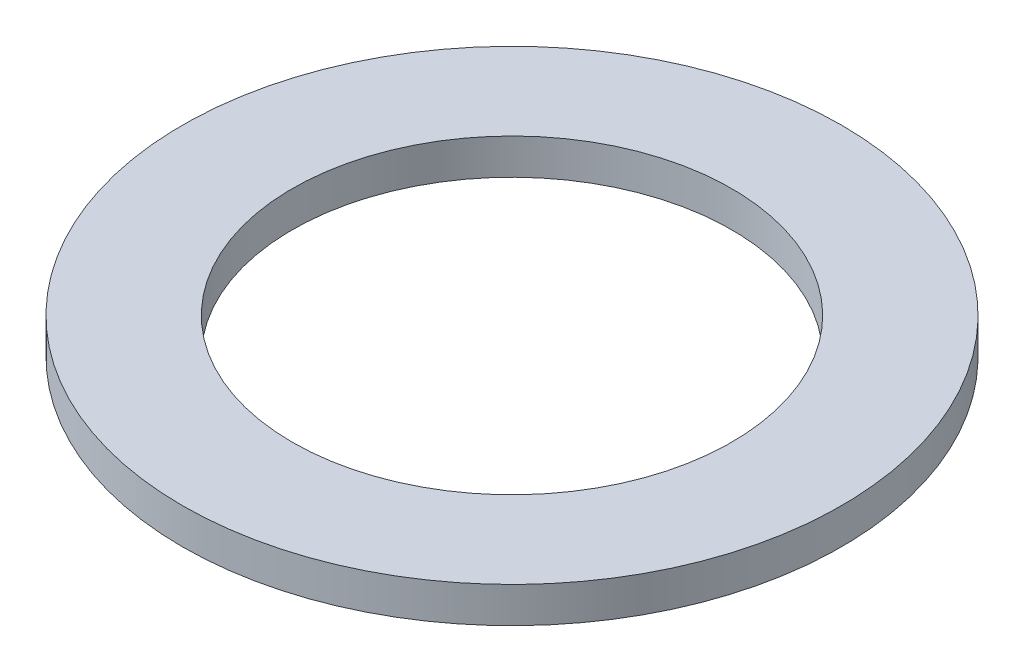
SolidWorks part; units mm, degrees
ref_plane "Front Plane" through (0, 0, 0) normal (0, 0, 1) x (1, 0, 0)
ref_plane "Top Plane" through (0, 0, 0) normal (0, 1, 0) x (1, 0, 0)
ref_plane "Right Plane" through (0, 0, 0) normal (1, 0, 0) x (0, 0, -1)
sketch "Sketch1" plane through (0, 0, 0) normal (0, 1, 0) x (1, 0, 0)
  circle A0 centre (0, 0) radius 12
  circle A1 centre (0, 0) radius 8
  dimension "D1" = 16
  dimension "D2" = 24
extrude "Boss-Extrude1" add sketch "Sketch1" along normal blind 1.3
